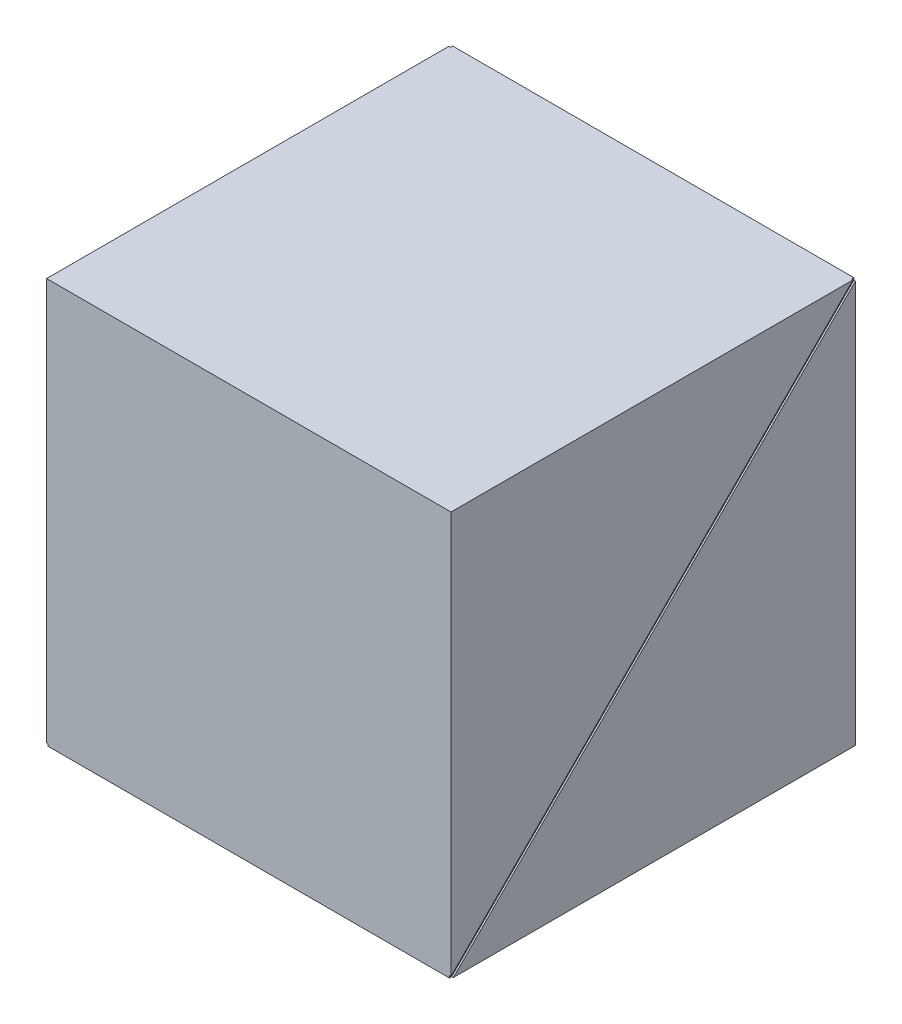
SolidWorks part; units mm, degrees
ref_plane "前视基准面" through (0, 0, 0) normal (0, 0, 1) x (1, 0, 0)
ref_plane "上视基准面" through (0, 0, 0) normal (0, 1, 0) x (1, 0, 0)
ref_plane "右视基准面" through (0, 0, 0) normal (1, 0, 0) x (0, 0, -1)
sketch "草图1" plane through (0, 0, 0) normal (0, 1, 0) x (1, 0, 0)
  line L1 (-12.5, -12.5) -> (12.5, -12.5)
  line L2 (-12.5, -12.5) -> (-12.5, 12.5)
  line L3 (-12.5, 12.5) -> (12.5, 12.5)
  line L4 (12.5, -12.5) -> (12.5, 12.5)
  line L5 (-12.5, -12.5) -> (12.5, 12.5) construction
  line L6 (-12.5, 12.5) -> (12.5, -12.5) construction
  point P0 (0, 0)
  dimension "D1" = 25
  dimension "D2" = 25
extrude "凸台-拉伸1" add sketch "草图1" along normal blind 25
sketch "草图2" plane through (12.5, 0, 0) normal (1, 0, 0) x (0, 0, -1)
  line L0 (12.5, 0) -> (-12.5, 25) construction
  line L1 (12.5, 25) -> (-12.5, 0) construction
  line L2 (12.4293, 25.0707) -> (-12.5707, 0.0707)
  line L3 (12.5707, 24.9293) -> (-12.4293, -0.0707)
  line L4 (12.4293, 25.0707) -> (12.5707, 24.9293)
  line L5 (-12.5707, 0.0707) -> (-12.4293, -0.0707)
  dimension "D1" = 0.1
  dimension "D2" = 0.1
extrude "切除-拉伸1" cut sketch "草图2" against normal blind 0.1
sketch "草图3" plane through (-12.5, 0, 0) normal (-1, 0, 0) x (0, 0, 1)
  line L4 (12.5707, 0.0707) -> (-12.4293, 25.0707)
  line L5 (12.4293, -0.0707) -> (12.5707, 0.0707)
  line L6 (-12.5707, 24.9293) -> (12.4293, -0.0707)
  line L7 (-12.4293, 25.0707) -> (-12.5707, 24.9293)
  line L8 (12.5707, 0.0707) -> (-12.4293, 25.0707)
  line L9 (12.4293, -0.0707) -> (12.5707, 0.0707)
  line L10 (-12.5707, 24.9293) -> (12.4293, -0.0707)
  line L11 (-12.4293, 25.0707) -> (-12.5707, 24.9293)
  dimension "D1" = 0
extrude "切除-拉伸2" cut sketch "草图3" against normal blind 0.1
